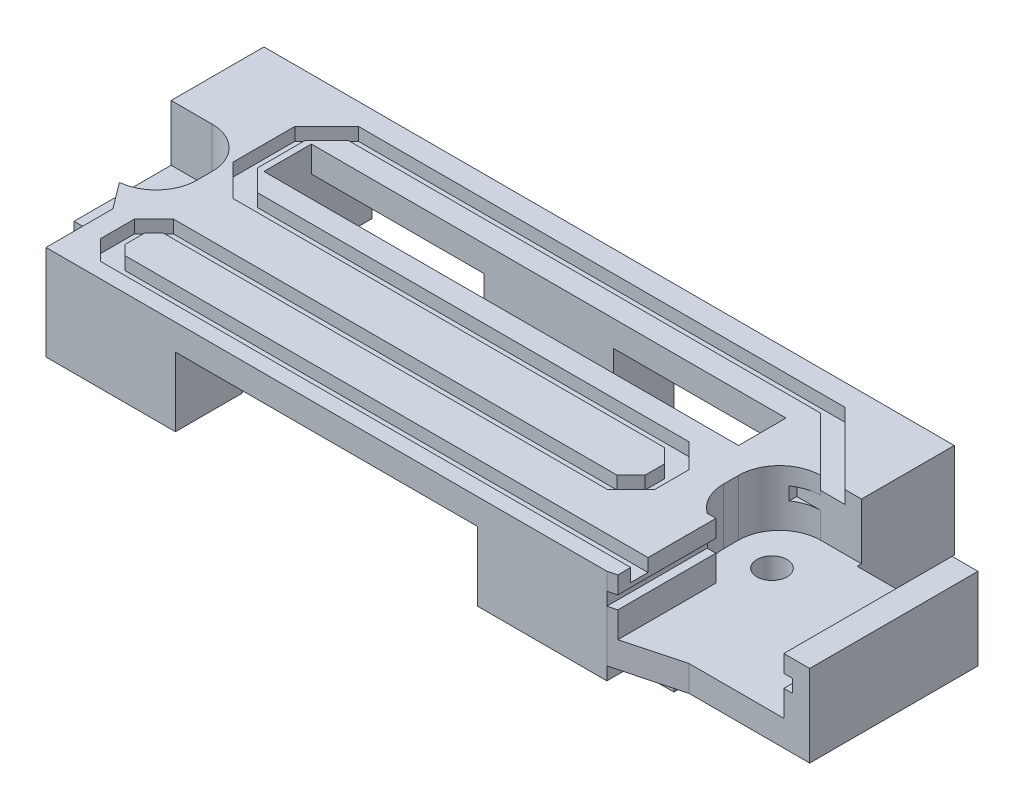
SolidWorks part; units mm, degrees
ref_plane "Front" through (0, 0, 0) normal (0, 0, 1) x (1, 0, 0)
ref_plane "Top" through (0, 0, 0) normal (0, 1, 0) x (1, 0, 0)
ref_plane "Right" through (0, 0, 0) normal (1, 0, 0) x (0, 0, -1)
sketch "Sketch1" plane through (0, 0, 0) normal (0, 1, 0) x (1, 0, 0)
  line L0 (0, 0) -> (-80, 0)
  line L4 (-7.5, -32.75) -> (-72.5, -32.75)
  line L5 (-72.5, -32.75) -> (-72.5, -25)
  line L7 (-80, -7.75) -> (-80, 0)
  line L11 (0, 0) -> (0, -7.75)
  line L16 (-7.5, -22) -> (-9.5, -22)
  line L19 (0, -7.75) -> (0, -10.75)
  line L20 (0, -10.75) -> (-9.5, -10.75)
  line L21 (-9.5, -10.75) -> (-9.5, -22)
  line L22 (-80, -7.75) -> (-80, -10.75)
  line L23 (-80, -10.75) -> (-70.5, -10.75)
  line L24 (-70.5, -10.75) -> (-70.5, -22)
  line L25 (-70.5, -22) -> (-74.75, -22)
  line L26 (-74.75, -22) -> (-72.5, -25)
  line L27 (-7.5, -22) -> (-7.5, -32.75)
  dimension "D1" = 80
  dimension "D3" = 32.75
  dimension "D4" = 7.75
  dimension "D5" = 7.75
  dimension "D9" = 9.5
  dimension "D10" = 9.5
  dimension "D7" = 2
  dimension "D11" = 4.25
  dimension "D13" = 3
  dimension "D14" = 2.25
  dimension "D15" = 11.25
  dimension "D2" = 3
  dimension "D6" = 3
extrude "Boss-Extrude1" add sketch "Sketch1" along normal blind 16
sketch "Sketch2" plane through (0, 0, 0) normal (0, -1, 0) x (1, 0, 0)
  line L0 (-72.5, 25) -> (-57.5, 25)
  line L1 (-7.5, 25) -> (-22.5, 25)
  line L2 (0, 7.75) -> (-12.5, 7.75)
  line L3 (-80, 7.75) -> (-67.5, 7.75)
  line L4 (-57.5, 25) -> (-57.5, 32.75)
  line L5 (-22.5, 25) -> (-22.5, 32.75)
  line L6 (-12.5, 7.75) -> (-12.5, 0)
  line L7 (-67.5, 7.75) -> (-67.5, 0)
  line L8 (0, 0) -> (0, 10.75)
  line L9 (0, 10.75) -> (-9.5, 10.75)
  line L10 (-7.5, 22) -> (-7.5, 32.75)
  line L11 (-7.5, 32.75) -> (-72.5, 32.75)
  line L12 (-72.5, 32.75) -> (-72.5, 25)
  line L13 (-72.5, 25) -> (-74.75, 22)
  line L14 (-80, 10.75) -> (-80, 0)
  line L15 (-80, 0) -> (0, 0)
  line L16 (0, 0) -> (0, 7.75)
  line L19 (-7.5, 32.75) -> (-72.5, 32.75)
  line L20 (-72.5, 32.75) -> (-72.5, 25)
  line L22 (-80, 7.75) -> (-80, 0)
  line L23 (-80, 0) -> (0, 0)
  line L24 (-67.5, 7.75) -> (-67.5, 25)
  line L25 (-12.5, 7.75) -> (-12.5, 25)
  line L26 (-57.5, 25) -> (-22.5, 25)
  line L37 (-9.5, 10.75) -> (-9.5, 22)
  line L38 (-9.5, 10.75) -> (-9.5, 22)
  line L41 (-9.5, 22) -> (-7.5, 22)
  line L42 (-9.5, 22) -> (-7.5, 22)
  line L43 (-7.5, 22) -> (-7.5, 32.75)
  line L48 (-72.5, 25) -> (-74.75, 22)
  line L49 (-74.75, 22) -> (-70.5, 22)
  line L50 (-74.75, 22) -> (-70.5, 22)
  line L51 (-70.5, 22) -> (-70.5, 10.75)
  line L52 (-70.5, 22) -> (-70.5, 10.75)
  line L53 (-70.5, 10.75) -> (-80, 10.75)
  dimension "D2" = 15
  dimension "D3" = 12.5
  dimension "D4" = 7.75
  dimension "D1" = 0
extrude "Cut-Extrude1" cut sketch "Sketch2" against normal blind 5
sketch "Sketch5" plane through (0, 0, 0) normal (0, -1, 0) x (1, 0, 0)
  line L0 (-67.5, 7.75) -> (-67.5, 25)
  line L1 (-12.5, 7.75) -> (-12.5, 25)
  line L12 (-80, 7.75) -> (-67.5, 7.75)
  line L13 (-67.5, 7.75) -> (-67.5, 0)
  line L14 (-67.5, 0) -> (-12.5, 0)
  line L15 (-12.5, 0) -> (-12.5, 7.75)
  line L18 (-7.5, 25) -> (-22.5, 25)
  line L19 (-22.5, 25) -> (-22.5, 32.75)
  line L20 (-22.5, 32.75) -> (-57.5, 32.75)
  line L21 (-57.5, 32.75) -> (-57.5, 25)
  line L22 (-57.5, 25) -> (-72.5, 25)
  line L23 (-72.5, 25) -> (-74.75, 22)
  line L24 (-80, 7.75) -> (-67.5, 7.75)
  line L25 (-67.5, 7.75) -> (-67.5, 0)
  line L26 (-67.5, 0) -> (-12.5, 0)
  line L27 (-12.5, 0) -> (-12.5, 7.75)
  line L30 (-7.5, 25) -> (-22.5, 25)
  line L31 (-22.5, 25) -> (-22.5, 32.75)
  line L32 (-22.5, 32.75) -> (-57.5, 32.75)
  line L33 (-57.5, 32.75) -> (-57.5, 25)
  line L34 (-57.5, 25) -> (-72.5, 25)
  line L44 (-12.5, 7.75) -> (0, 7.75)
  line L45 (-12.5, 7.75) -> (0, 7.75)
  line L46 (0, 10.75) -> (-9.5, 10.75)
  line L47 (0, 10.75) -> (-9.5, 10.75)
  line L48 (-72.5, 25) -> (-74.75, 22)
  line L49 (-74.75, 22) -> (-70.5, 22)
  line L50 (-74.75, 22) -> (-70.5, 22)
  line L51 (-70.5, 22) -> (-70.5, 10.75)
  line L52 (-70.5, 22) -> (-70.5, 10.75)
  line L53 (-9.5, 10.75) -> (-9.5, 22)
  line L54 (-9.5, 10.75) -> (-9.5, 22)
  line L55 (-9.5, 22) -> (-7.5, 22)
  line L56 (-9.5, 22) -> (-7.5, 22)
  line L57 (0, 7.75) -> (0, 10.75)
  line L58 (0, 7.75) -> (0, 10.75)
  line L59 (-7.5, 22) -> (-7.5, 25)
  line L60 (-7.5, 22) -> (-7.5, 25)
  line L61 (-70.5, 10.75) -> (-80, 10.75)
  line L62 (-70.5, 10.75) -> (-80, 10.75)
  line L63 (-80, 10.75) -> (-80, 7.75)
  line L64 (-80, 10.75) -> (-80, 7.75)
  line M16 (-67.5, 7.75) -> (-67.5, 0)
  line M17 (-67.5, 0) -> (-12.5, 0)
  line M18 (-12.5, 0) -> (-12.5, 7.75)
  line M21 (-7.5, 25) -> (-22.5, 25)
  line M22 (-22.5, 25) -> (-22.5, 32.75)
  line M23 (-22.5, 32.75) -> (-57.5, 32.75)
  line M24 (-57.5, 32.75) -> (-57.5, 25)
  line M25 (-57.5, 25) -> (-72.5, 25)
  dimension "D1" = 0
extrude "Cut-Extrude4" cut sketch "Sketch5" against normal blind 13 contours L1 L0 M18 M21 M22 M23 M24 M25 M16 M17
sketch "Sketch6" plane through (0, 13, 0) normal (0, -1, 0) x (1, 0, 0)
  line L0 (-12.5, 7) -> (-67.5, 7)
  line L1 (-12.5, 12.5) -> (-67.5, 12.5)
  line L8 (-12.5, 0) -> (-12.5, 25)
  line L9 (-12.5, 25) -> (-22.5, 25)
  line L10 (-22.5, 25) -> (-22.5, 32.75)
  line L11 (-22.5, 32.75) -> (-57.5, 32.75)
  line L12 (-57.5, 32.75) -> (-57.5, 25)
  line L13 (-57.5, 25) -> (-67.5, 25)
  line L14 (-67.5, 25) -> (-67.5, 0)
  line L15 (-67.5, 0) -> (-12.5, 0)
  line L17 (-12.5, 25) -> (-22.5, 25)
  line L18 (-22.5, 25) -> (-22.5, 32.75)
  line L19 (-22.5, 32.75) -> (-57.5, 32.75)
  line L20 (-57.5, 32.75) -> (-57.5, 25)
  line L21 (-57.5, 25) -> (-67.5, 25)
  line L22 (-67.5, 25) -> (-67.5, 0)
  line L23 (-67.5, 0) -> (-12.5, 0)
  line L27 (-12.5, 0) -> (-12.5, 25)
  line M11 (-12.5, 0) -> (-12.5, 25)
  line M17 (-67.5, 25) -> (-67.5, 0)
  dimension "D2" = 7
  dimension "D3" = 12.5
  dimension "D1" = 0
extrude "Cut-Extrude5" cut sketch "Sketch6" against normal up to surface (3 mm away) contours L1 L0 M11 M17 up to face at (-42.6731, 16, 17.0385)
sketch "Sketch7" plane through (0, 13, 0) normal (0, -1, 0) x (1, 0, 0)
  line L0 (-47.5, 0) -> (-47.5, 7)
  line L2 (-67.5, 0) -> (-12.5, 0) construction
  line L3 (-12.5, 7) -> (-67.5, 7) construction
  line L4 (-32.5, 0) -> (-32.5, 7)
  line L5 (-32.5, 12.5) -> (-32.5, 15.5)
  line L6 (-12.5, 12.5) -> (-67.5, 12.5) construction
  line L7 (-32.5, 15.5) -> (-47.5, 15.5)
  line L8 (-47.5, 15.5) -> (-47.5, 12.5)
  line L9 (-12.5, 12.5) -> (-67.5, 12.5)
  line L10 (-67.5, 0) -> (-12.5, 0)
  line L11 (-12.5, 7) -> (-67.5, 7)
  point P14 (-40, 0)
  dimension "D1" = 7.5
  dimension "D2" = 7.5
  dimension "D3" = 3
extrude "Boss-Extrude2" add sketch "Sketch7" along normal blind 13.25
sketch "Sketch8" plane through (0, 0, 0) normal (0, 0, -1) x (-1, 0, 0)
  line L0 (47.5, -0.25) -> (32.5, -0.25) construction
  line L1 (47.5, -0.25) -> (32.5, -0.25)
  circle A0 centre (40, -0.25) radius 2.5
  dimension "D5" = 5
extrude "Cut-Extrude6" cut sketch "Sketch8" against normal up to surface (15.5 mm away) up to face at (-40, 6.375, 15.5)
sketch "Sketch9" plane through (-32.5, 0, 0) normal (1, 0, 0) x (0, 0, -1)
  line L0 (0, -0.25) -> (-7, -0.25) construction
  line L3 (-3.5, 3.25) -> (-3.5, -0.25)
  circle A0 centre (-3.5, 3.25) radius 1.75
  dimension "D2" = 3.5
  dimension "D1" = 3.5
extrude "Cut-Extrude7" cut sketch "Sketch9" against normal up to surface (15 mm away) up to face at (-47.5, 6.375, 3.5)
ref_plane "Plane1" through (0, 6.5, 0) normal (0, -1, 0) x (-1, 0, 0)
sketch "Sketch11" plane through (0, 6.5, 0) normal (0, -1, 0) x (-1, 0, 0)
  line L0 (70.5, -22) -> (74.75, -22) construction
  line L1 (70.5, -10.75) -> (70.5, -22) construction
  line L2 (80, -10.75) -> (70.5, -10.75) construction
  line L3 (70.5, -22) -> (74.75, -22)
  line L4 (70.5, -10.75) -> (70.5, -22)
  line L5 (80, -10.75) -> (70.5, -10.75)
  line L7 (74.75, -22) -> (72.5, -25) construction
  line L8 (74.75, -22) -> (72.5, -25)
  line L10 (74.75, -22) -> (80, -22)
  line L12 (80, -22) -> (80, -10.75)
  line L13 (7.5, -22) -> (9.5, -22) construction
  line L14 (9.5, -22) -> (9.5, -10.75) construction
  line L15 (9.5, -10.75) -> (0, -10.75) construction
  line L16 (7.5, -22) -> (9.5, -22)
  line L17 (9.5, -22) -> (9.5, -10.75)
  line L18 (9.5, -10.75) -> (0, -10.75)
  line L26 (-14, -11.25) -> (-14, -30.75)
  line L27 (-14, -30.75) -> (0, -30.75)
  line L28 (7.5, -32.75) -> (0, -30.75)
  line L29 (0, -10.75) -> (0, -11.25)
  line L30 (7.5, -32.75) -> (7.5, -22) construction
  line L31 (0, -11.25) -> (-14, -11.25)
  line L32 (7.5, -32.75) -> (7.5, -22)
  circle A0 centre (75.25, -16.375) radius 1.75
  circle A1 centre (4.75, -16.375) radius 1.75
  dimension "D1" = 3.5
  dimension "D2" = 11.25
  dimension "D3" = 5.625
  dimension "D4" = 4.75
  dimension "D5" = 9.5
  dimension "D6" = 11.25
  dimension "D7" = 9.5
  dimension "D8" = 4.75
  dimension "D9" = 5.625
  dimension "D10" = 19.5
  dimension "D12" = 9.5
  dimension "D13" = 0.5
  dimension "D11" = 14
extrude "Boss-Extrude3" add sketch "Sketch11" against normal blind 3
sketch "Sketch12" plane through (0, 9.5, 0) normal (0, 1, 0) x (1, 0, 0)
  line L0 (-74.75, -22) -> (-80, -22) construction
  line L1 (-70.5, -10.75) -> (-70.5, -22) construction
  line L2 (-80, -10.75) -> (-70.5, -10.75) construction
  line L3 (-74.75, -22) -> (-80, -22)
  line L4 (-70.5, -10.75) -> (-70.5, -22)
  line L5 (-80, -10.75) -> (-70.5, -10.75)
  line L6 (-70.5, -22) -> (-74.75, -22) construction
  line L7 (-74.75, -22) -> (-74.75, -21.9736)
  line L8 (11, -30.75) -> (11, -11.25)
  line L9 (-7.5, -21.123) -> (-6.5, -21.123)
  line L10 (0, -11.25) -> (0, -10.75)
  line L11 (0, -10.75) -> (-9.5, -10.75)
  line L12 (-9.5, -10.75) -> (-9.5, -22)
  line L13 (-9.5, -22) -> (-7.5, -22)
  line L14 (-7.5, -22) -> (-7.5, -32.75)
  line L15 (-7.5, -22) -> (-7.5, -32.75)
  line L16 (-7.5, -32.75) -> (0, -30.75)
  line L17 (0, -30.75) -> (14, -30.75)
  line L18 (14, -30.75) -> (14, -11.25)
  line L19 (14, -11.25) -> (0, -11.25)
  line L20 (0, -11.25) -> (0, -10.75)
  line L21 (0, -10.75) -> (-9.5, -10.75)
  line L22 (-9.5, -10.75) -> (-9.5, -22)
  line L23 (-9.5, -22) -> (-7.5, -22)
  line L26 (-7.5, -32.75) -> (0, -30.75)
  line L27 (0, -30.75) -> (14, -30.75)
  line L28 (14, -30.75) -> (14, -11.25)
  line L29 (14, -11.25) -> (0, -11.25)
  line L30 (-6.5, -21.123) -> (-6.5, -32.4833)
  line L33 (-7.5, -22) -> (-7.5, -21.123)
  line L34 (-70.5, -22) -> (-74.75, -22)
  arc A0 (-4.75, -10.75) -> (-9.5, -15.5) centre (-4.75, -15.5) ccw
  arc A1 (-9.5, -17.25) -> (-7.5, -21.123) centre (-4.75, -17.25) ccw
  arc A4 (-70.5, -15.5) -> (-75.25, -10.75) centre (-75.25, -15.5) ccw
  arc A5 (-75.25, -22) -> (-70.5, -17.25) centre (-75.25, -17.25) ccw
  circle A6 centre (-4.75, -16.375) radius 1.75 construction
  circle A7 centre (-75.25, -16.375) radius 1.75 construction
  circle A8 centre (-4.75, -16.375) radius 1.75
  circle A9 centre (-75.25, -16.375) radius 1.75
  dimension "D2" = 3
  dimension "D3" = 1
  dimension "D1" = 0
extrude "Boss-Extrude4" add sketch "Sketch12" along normal up to surface (6.5 mm away) up to face at (-40, 16, 9.75)
ref_plane "Plane2" through (0, 0, 32.75) normal (0, 0, 1) x (1, 0, 0)
sketch "Sketch13" plane through (0, 0, 32.75) normal (0, 0, 1) x (1, 0, 0)
  line L0 (11, 16) -> (11, 9.5) construction
  line L1 (-7.5, 6.5) -> (-7.5, 5) construction
  line L3 (11, 9.5) -> (0, 9.5) construction
  line L4 (11, 16) -> (11, 9.5)
  line L5 (-7.5, 6.5) -> (-7.5, 5)
  line L7 (11, 9.5) -> (0, 9.5)
  line L9 (-7.5, 14) -> (12, 14)
  line L10 (-7.5, 14) -> (-7.5, 12.5)
  line L11 (-7.5, 12.5) -> (12, 12.5)
  line L12 (12, 14) -> (12, 12.5)
  dimension "D1" = 19.5
  dimension "D2" = 1.5
  dimension "D3" = 1
  dimension "D4" = 3
extrude "Cut-Extrude9" cut sketch "Sketch13" against normal up to surface (22 mm away) contours L5 L11 L4 L9 | L12 L9 L4 L11 | L10 L11 L5 L9 up to face at (-2.375, 12.75, 10.75)
sketch "Sketch14" plane through (0, 16, 0) normal (0, 1, 0) x (1, 0, 0)
  line L0 (-1.9216, -10.75) -> (-10.1716, -2.5)
  line L1 (-4.75, -10.75) -> (-11, -4.5)
  line L2 (-11, -4.5) -> (-65.7257, -4.5)
  line L3 (-65.7257, -4.5) -> (-68.2243, -6.9985)
  line L4 (-68.2243, -6.9985) -> (-68.2243, -12.5015)
  line L5 (-68.2243, -12.5015) -> (-65.7257, -15)
  line L6 (-65.7257, -15) -> (-15.7257, -15)
  line L7 (-10.1716, -2.5) -> (-66.5542, -2.5)
  line L8 (-66.5542, -2.5) -> (-70.2243, -6.1701)
  line L9 (-70.2243, -6.1701) -> (-70.2243, -13.3299)
  line L10 (-70.2243, -13.3299) -> (-66.5542, -17)
  line L11 (-66.5542, -17) -> (-16.5542, -17)
  line L12 (-16.5542, -17) -> (-14.9397, -18.6145)
  line L13 (-14.9397, -18.6145) -> (-14.9397, -20.8977)
  line L14 (-9.5, -17.25) -> (-9.5, -15.5)
  line L15 (-4.75, -10.75) -> (0, -10.75)
  line L16 (0, -10.75) -> (0, 0)
  line L17 (0, 0) -> (-80, 0)
  line L18 (-80, 0) -> (-80, -10.75)
  line L19 (-80, -10.75) -> (-75.25, -10.75)
  line L20 (-70.5, -15.5) -> (-70.5, -17.25)
  line L21 (-74.75, -21.9736) -> (-74.75, -22)
  line L22 (-74.75, -22) -> (-72.5, -25)
  line L23 (-72.5, -25) -> (-72.5, -32.75)
  line L24 (-72.5, -32.75) -> (-7.5, -32.75)
  line L25 (-7.5, -32.75) -> (-6.5, -32.4833)
  line L26 (-6.5, -32.4833) -> (-6.5, -21.123)
  line L27 (-6.5, -21.123) -> (-7.5, -21.123)
  line L28 (-9.5, -17.25) -> (-9.5, -15.5)
  line L29 (-4.75, -10.75) -> (0, -10.75)
  line L30 (0, -10.75) -> (0, 0)
  line L31 (0, 0) -> (-80, 0)
  line L32 (-80, 0) -> (-80, -10.75)
  line L33 (-80, -10.75) -> (-75.25, -10.75)
  line L34 (-70.5, -15.5) -> (-70.5, -17.25)
  line L35 (-74.75, -21.9736) -> (-74.75, -22)
  line L36 (-74.75, -22) -> (-72.5, -25)
  line L37 (-72.5, -25) -> (-72.5, -32.75)
  line L38 (-72.5, -32.75) -> (-7.5, -32.75)
  line L39 (-7.5, -32.75) -> (-6.5, -32.4833)
  line L40 (-6.5, -32.4833) -> (-6.5, -21.123)
  line L41 (-6.5, -21.123) -> (-7.5, -21.123)
  line L42 (-15.7257, -24.5122) -> (-67.1266, -24.5122)
  line L43 (-38.3629, -2.5) -> (-38.3629, 0)
  line L44 (-38.3629, -4.5) -> (-38.3629, -7)
  line L45 (-67.1266, -24.5122) -> (-68.2243, -25.6099)
  line L46 (-68.2243, -25.6099) -> (-68.2243, -27.8932)
  line L47 (-67.5, -7) -> (-12.5, -7) construction
  line L48 (-67.5, -7) -> (-12.5, -7)
  line L49 (-67.5, -7) -> (-67.5, -12.5) construction
  line L50 (-67.5, -9.75) -> (-68.2243, -9.75)
  line L51 (-70.2243, -13.3299) -> (-70.8892, -13.617)
  line L52 (-68.2243, -27.8932) -> (-67.1266, -28.9909)
  line L53 (-67.1266, -28.9909) -> (-6.5, -28.9909)
  line L54 (-16.5542, -22.5122) -> (-67.955, -22.5122)
  line L55 (-67.955, -22.5122) -> (-70.2243, -24.7815)
  line L56 (-70.2243, -24.7815) -> (-70.2243, -28.7216)
  line L57 (-70.2243, -28.7216) -> (-67.955, -30.9909)
  line L58 (-67.955, -30.9909) -> (-6.5, -30.9909)
  line L59 (-14.9397, -20.8977) -> (-16.5542, -22.5122)
  line L60 (-15.7257, -24.5122) -> (-12.9397, -21.7262)
  line L61 (-12.9397, -21.7262) -> (-12.9397, -17.7861)
  line L62 (-12.9397, -17.7861) -> (-15.7257, -15)
  arc A4 (-9.5, -17.25) -> (-7.5, -21.123) centre (-4.75, -17.25) ccw
  arc A5 (-4.75, -10.75) -> (-9.5, -15.5) centre (-4.75, -15.5) ccw
  arc A6 (-70.5, -15.5) -> (-75.25, -10.75) centre (-75.25, -15.5) ccw
  arc A7 (-74.75, -21.9736) -> (-70.5, -17.25) centre (-75.25, -17.25) ccw
  arc A8 (-9.5, -17.25) -> (-7.5, -21.123) centre (-4.75, -17.25) ccw
  arc A9 (-4.75, -10.75) -> (-9.5, -15.5) centre (-4.75, -15.5) ccw
  arc A10 (-70.5, -15.5) -> (-75.25, -10.75) centre (-75.25, -15.5) ccw
  arc A11 (-74.75, -21.9736) -> (-70.5, -17.25) centre (-75.25, -17.25) ccw
  point P62 (-15.7469, -17.8072)
  point P63 (-15.7469, -21.705)
  dimension "D7" = 2
  dimension "D2" = 2
  dimension "D3" = 2
  dimension "D4" = 45
  dimension "D5" = 2
  dimension "D6" = 2
  dimension "D12" = 2
  dimension "D8" = 2
  dimension "D9" = 2
  dimension "D10" = 2
  dimension "D11" = 50
  dimension "D13" = 2
  dimension "D14" = 2
  dimension "D15" = 2
  dimension "D16" = 2
  dimension "D17" = 2
extrude "Cut-Extrude10" cut sketch "Sketch14" against normal blind 1.5
equation "\"D10@Sketch1\"=\"D9@Sketch1\""
equation "\"D4@Sketch11\"=\"D5@Sketch11\"/2"
equation "\"D8@Sketch11\"=\"D7@Sketch11\"/2"
equation "\"D9@Sketch11\"=\"D6@Sketch11\"/2"
equation "\"D12@Sketch11\"=\"D7@Sketch11\""
equation "\"D6@Sketch1\"=\"D2@Sketch1\""
equation "\"D6@Sketch14\"=\"D3@Sketch14\""
equation "\"D5@Sketch14\"=\"D3@Sketch14\""
equation "\"D2@Sketch14\"=\"D3@Sketch14\""
equation "\"D7@Sketch14\"=\"D3@Sketch14\""
equation "\"D12@Sketch14\"=\"D3@Sketch14\""
equation "\"D8@Sketch14\"=\"D3@Sketch14\""
equation "\"D9@Sketch14\"=\"D3@Sketch14\""
equation "\"D10@Sketch14\"=\"D3@Sketch14\""
equation "\"D13@Sketch14\"=\"D3@Sketch14\""
equation "\"D14@Sketch14\"=\"D3@Sketch14\""
equation "\"D15@Sketch14\"=\"D3@Sketch14\""
equation "\"D16@Sketch14\"=\"D3@Sketch14\""
equation "\"D17@Sketch14\"=\"D3@Sketch14\""
